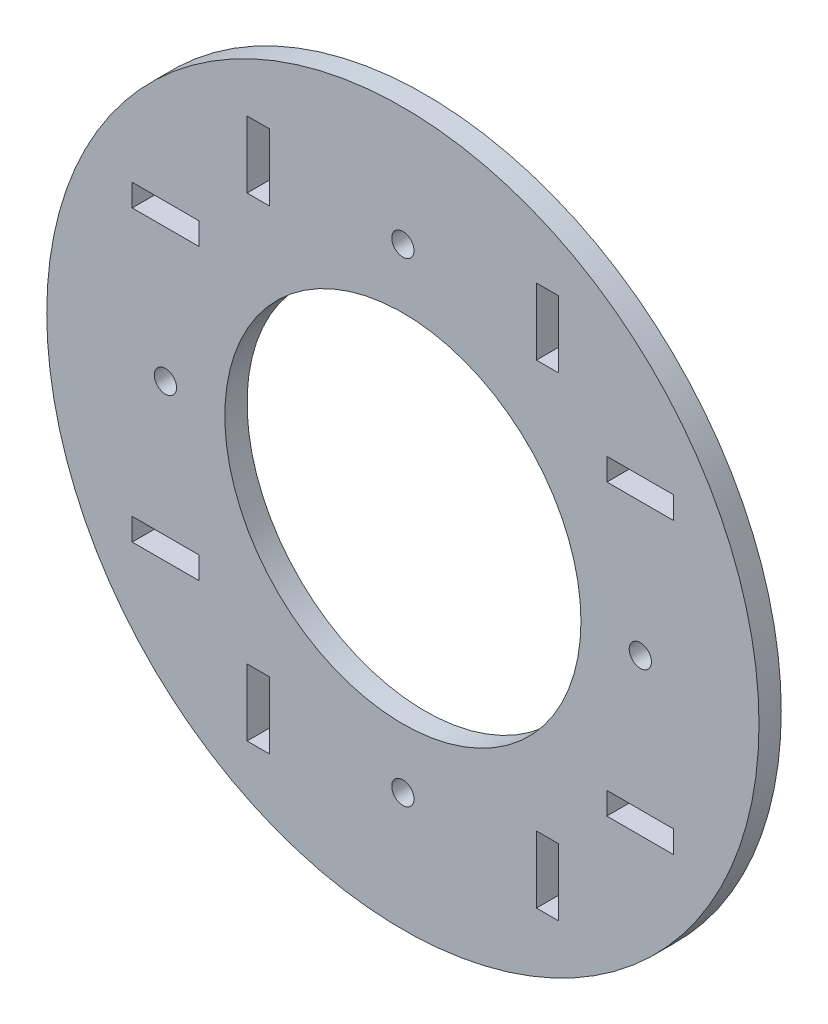
SolidWorks part; units mm, degrees
material "ABS"
ref_plane "Front Plane" through (0, 0, 0) normal (0, 0, 1) x (1, 0, 0)
ref_plane "Top Plane" through (0, 0, 0) normal (0, 1, 0) x (1, 0, 0)
ref_plane "Right Plane" through (0, 0, 0) normal (1, 0, 0) x (0, 0, -1)
sketch "Sketch1" plane through (0, 0, 0) normal (0, 0, 1) x (1, 0, 0)
  line L0 (-32.2567, -22.225) -> (-41.7817, -22.225)
  line L1 (25.9093, -22.225) -> (-32.2567, -22.225) construction
  line L2 (-3.1737, -22.225) -> (-3.1737, 0) construction
  line L3 (-41.7817, -22.225) -> (-41.7817, -19.05)
  line L4 (-41.7817, -19.05) -> (-32.2567, -19.05)
  line L5 (-32.2567, -19.05) -> (-32.2567, -22.225)
  line L6 (-41.7817, 22.225) -> (-41.7817, 19.05)
  line L7 (-32.2567, 22.225) -> (-41.7817, 22.225)
  line L8 (-32.2567, 19.05) -> (-32.2567, 22.225)
  line L9 (-41.7817, 19.05) -> (-32.2567, 19.05)
  line L10 (-3.1737, 0) -> (-25.3987, 0) construction
  line L11 (-25.3987, 0) -> (-25.3987, 29.083) construction
  line L12 (-25.3987, 29.083) -> (-25.3987, 38.608)
  line L13 (22.2408, 0) -> (-3.1737, 0) construction
  line L14 (-25.3987, 38.608) -> (-22.2237, 38.608)
  line L15 (-22.2237, 38.608) -> (-22.2237, 29.083)
  line L16 (-22.2237, 29.083) -> (-25.3987, 29.083)
  line L17 (19.0513, 38.608) -> (15.8763, 38.608)
  line L18 (15.8763, 29.083) -> (19.0513, 29.083)
  line L19 (15.8763, 38.608) -> (15.8763, 29.083)
  line L20 (19.0513, 29.083) -> (19.0513, 38.608)
  line L21 (15.8763, -29.083) -> (19.0513, -29.083)
  line L22 (19.0513, -29.083) -> (19.0513, -38.608)
  line L23 (19.0513, -38.608) -> (15.8763, -38.608)
  line L24 (15.8763, -38.608) -> (15.8763, -29.083)
  line L25 (-22.2237, -29.083) -> (-25.3987, -29.083)
  line L26 (-25.3987, -29.083) -> (-25.3987, -38.608)
  line L27 (-25.3987, -38.608) -> (-22.2237, -38.608)
  line L28 (35.4343, -22.225) -> (35.4343, -19.05)
  line L29 (25.9093, -22.225) -> (35.4343, -22.225)
  line L30 (-22.2237, -38.608) -> (-22.2237, -29.083)
  line L32 (25.9093, -19.05) -> (25.9093, -22.225)
  line L33 (35.4343, -19.05) -> (25.9093, -19.05)
  line L34 (35.4597, 22.225) -> (35.4597, 19.05)
  line L35 (25.9347, 22.225) -> (35.4597, 22.225)
  line L36 (35.4597, 19.05) -> (25.9347, 19.05)
  line L37 (25.9347, 19.05) -> (25.9347, 22.225)
  circle A0 centre (-3.1737, 0) radius 50.8
  circle A1 centre (-3.1737, 0) radius 25.4
  circle A2 centre (-3.1737, -33.8709) radius 1.5875
  circle A3 centre (30.6972, 0) radius 1.5875
  circle A4 centre (-37.0446, 0) radius 1.5875
  circle A5 centre (-3.1737, 33.8709) radius 1.5875
  point P48 (-3.1737, 0)
  dimension "D1" = 9.525
  dimension "D2" = 50.8
  dimension "D3" = 3.175
  dimension "D5" = 3.175
  dimension "D6" = 101.6
  dimension "D4" = 58.166
  dimension "D7" = 22.225
  dimension "D8" = 29.083
  dimension "D9" = 9.525
  dimension "D10" = 3.175
  dimension "D11" = 4
extrude "Boss-Extrude1" add sketch "Sketch1" along normal blind 3.175
